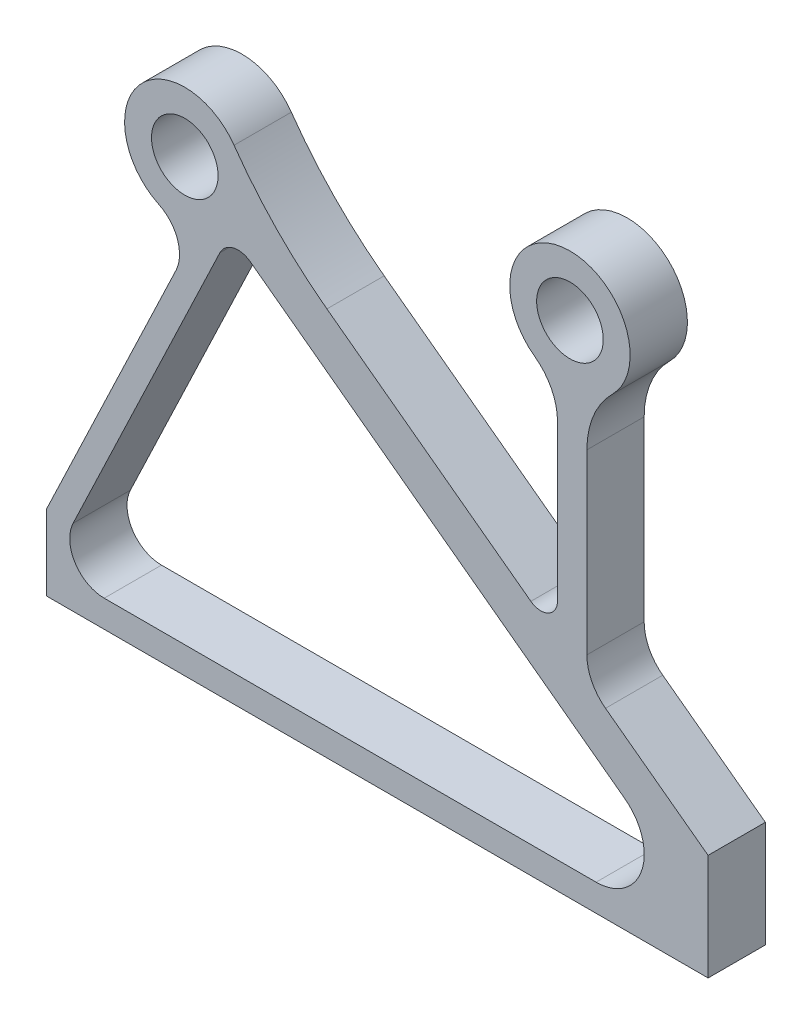
SolidWorks part; units mm, degrees
ref_plane "Front Plane" through (0, 0, 0) normal (0, 0, 1) x (1, 0, 0)
ref_plane "Top Plane" through (0, 0, 0) normal (0, 1, 0) x (1, 0, 0)
ref_plane "Right Plane" through (0, 0, 0) normal (1, 0, 0) x (0, 0, -1)
sketch "Szkic1" [suppressed] plane through (0, 0, 0) normal (0, 0, 1) x (1, 0, 0)
  line L5 (0, 0) -> (462, 0)
  line L6 (0, 0) -> (0, 400)
  line L7 (0, 400) -> (462, 400)
  line L8 (462, 0) -> (462, 400)
  circle A0 centre (96.5, 314) radius 23.25
  circle A1 centre (365.5, 349.5) radius 23.25
  dimension "D3" = 46.5
  dimension "D4" = 46.5
  dimension "D1" = 400
  dimension "D2" = 462
  dimension "D5" = 96.5
  dimension "D6" = 269
  dimension "D7" = 314
  dimension "D8" = 349.5
extrude "Dodanie-wyciągnięcie1" [suppressed] add sketch "Szkic1" along normal blind 40
other "Grafika1" [suppressed]
other "Grafika (Zamknięta) -1" [suppressed]
other "Grafika (Zamknięta) -2" [suppressed]
other "Grafika (Zamknięta) -3" [suppressed]
other "Grafika (Zamknięta) -4" [suppressed]
other "Grafika (Zamknięta) -5" [suppressed]
other "Grafika (Zamknięta) -6" [suppressed]
sketch "Szkic2" plane through (0, 0, 0) normal (0, 0, 1) x (1, 0, 0)
  line L0 (356.8087, 284.0851) -> (356.8087, 175.3102)
  line L1 (338.2089, 165.9466) -> (195.7579, 271.5714)
  line L2 (377.3332, 277.1044) -> (377.3332, 153.1163)
  line L3 (390.3298, 127.2999) -> (461.9781, 74.174)
  line L4 (461.9781, 74.174) -> (462, 0)
  line L5 (462, 0) -> (0, 0)
  line L6 (90.3406, 242.1447) -> (0, 52.7883)
  line L7 (0, 52.7883) -> (0, 0)
  line L8 (142.2103, 273.3981) -> (403.7882, 79.4429)
  line L9 (383.7711, 18.8392) -> (40.2234, 18.8392)
  line L10 (18.4911, 53.2864) -> (120.986, 268.1184)
  circle A0 centre (96.5, 314) radius 23.25
  circle A1 centre (365.5, 349.5) radius 23.25
  arc A2 (130.9125, 338.1423) -> (78.3505, 276.0835) centre (96.5, 314) ccw
  arc A3 (395.0726, 319.6248) -> (340.8037, 315.483) centre (365.5, 349.5) ccw
  arc A4 (356.8087, 175.3102) -> (338.2089, 165.9466) centre (345.1519, 175.3102) cw
  arc A5 (377.3332, 153.1163) -> (390.3298, 127.2999) centre (409.4722, 153.1163) ccw
  arc A6 (120.986, 268.1184) -> (142.2103, 273.3981) centre (133.7723, 262.0181) cw
  arc A7 (403.7882, 79.4429) -> (383.7711, 18.8392) centre (383.7711, 52.4468) cw
  arc A8 (90.3406, 242.1447) -> (78.3505, 276.0835) centre (67.3544, 253.1113) ccw
  arc A9 (340.8037, 315.483) -> (356.8087, 284.0851) centre (318.0088, 284.0851) cw
  arc A10 (18.4911, 53.2864) -> (40.2234, 18.8392) centre (40.2234, 42.9181) ccw
  arc A11 (377.3332, 277.1044) -> (395.0726, 319.6248) centre (437.1622, 277.1044) cw
  arc A12 (130.9125, 338.1423) -> (195.7579, 271.5714) centre (368.9372, 505.1298) ccw
  point P4 (0, 0)
  point P13 (403.7882, 79.4429)
  point P41 (340.8037, 165.9466)
  point P44 (403.7882, 79.4429)
  dimension "D1" = 46.5
  dimension "D2" = 46.5
  dimension "D3" = 314
  dimension "D4" = 349.5
  dimension "D5" = 269
  dimension "D6" = 96.5
extrude "Dodanie-wyciągnięcie2" add sketch "Szkic2" along normal blind 40
